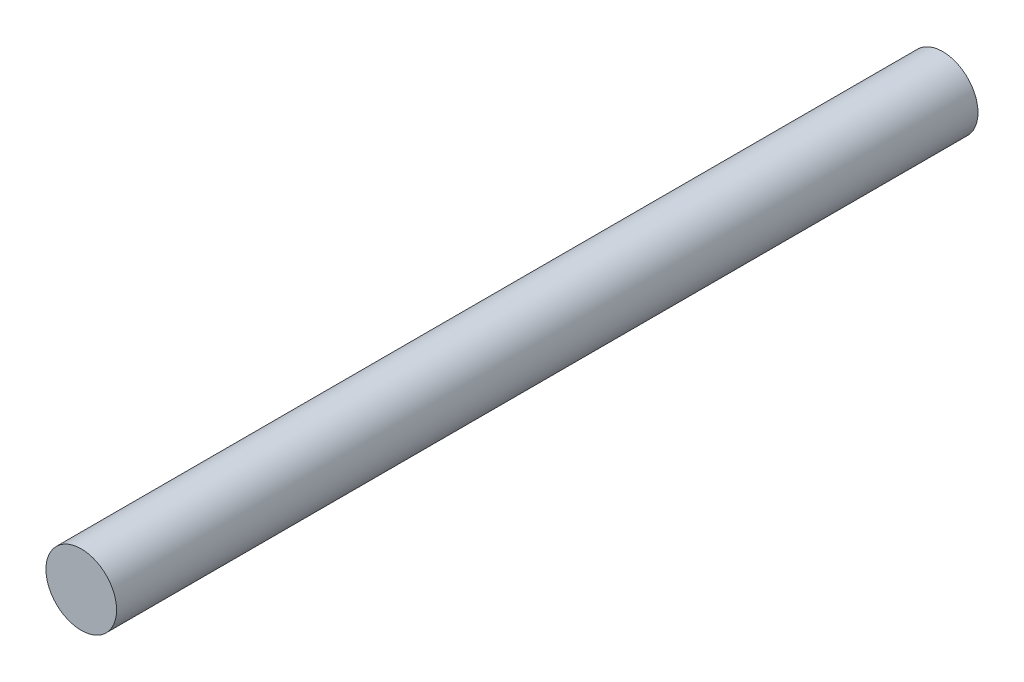
SolidWorks part; units mm, degrees
ref_plane "Front Plane" through (0, 0, 0) normal (0, 0, 1) x (1, 0, 0)
ref_plane "Top Plane" through (0, 0, 0) normal (0, 1, 0) x (1, 0, 0)
ref_plane "Right Plane" through (0, 0, 0) normal (1, 0, 0) x (0, 0, -1)
sketch "Sketch1" plane through (0, 0, 0) normal (0, 0, 1) x (1, 0, 0)
  line L1 (-25, 0) -> (25, 0) construction
  dimension "OD" = 50
sketch "Sketch2" plane through (0, 0, 0) normal (1, 0, 0) x (0, 0, -1)
  line L0 (304.8, 0) -> (-304.8, 0)
  point P4 (0, 0)
  dimension "Length" = 609.6
sketch "Sketch3" plane through (0, 0, 0) normal (0, 0, 1) x (1, 0, 0)
  circle A0 centre (0, 0) radius 25
extrude "Boss-Extrude1" add sketch "Sketch3" along normal up to vertex (304.8 mm away) and the other way up to vertex (304.8 mm away) up to point (0, 0, 304.8) other way up to point (0, 0, -304.8)
